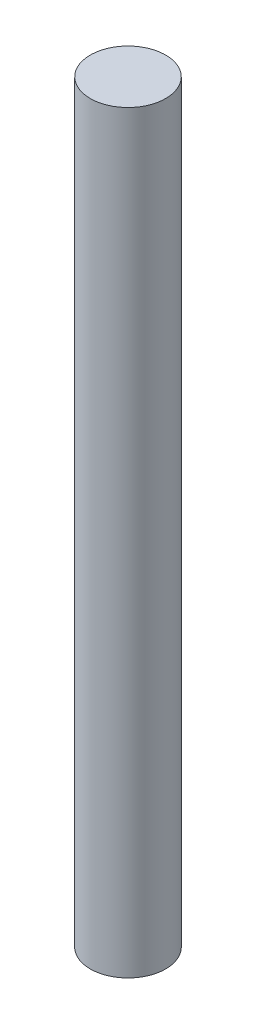
SolidWorks part; units mm, degrees
material "AISI 304"
ref_plane "Front Plane" through (0, 0, 0) normal (0, 0, 1) x (1, 0, 0)
ref_plane "Top Plane" through (0, 0, 0) normal (0, 1, 0) x (1, 0, 0)
ref_plane "Right Plane" through (0, 0, 0) normal (1, 0, 0) x (0, 0, -1)
sketch "Sketch1" plane through (0, 0, 0) normal (0, 1, 0) x (1, 0, 0)
  circle A0 centre (0, 0) radius 3
  dimension "D1" = 6
extrude "Boss-Extrude1" add sketch "Sketch1" along normal blind 60
